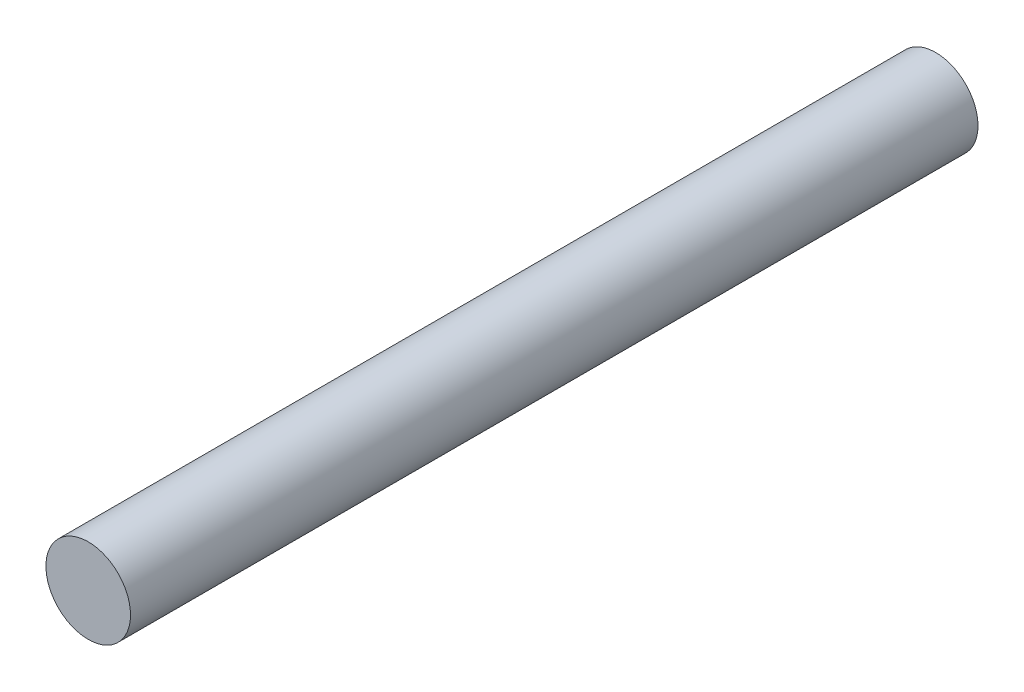
SolidWorks part; units mm, degrees
ref_plane "Front Plane" through (0, 0, 0) normal (0, 0, 1) x (1, 0, 0)
ref_plane "Top Plane" through (0, 0, 0) normal (0, 1, 0) x (1, 0, 0)
ref_plane "Right Plane" through (0, 0, 0) normal (1, 0, 0) x (0, 0, -1)
sketch "Sketch1" plane through (0, 0, 0) normal (0, 0, 1) x (1, 0, 0)
  circle A0 centre (0, 0) radius 1.27
extrude "Extrude1" add sketch "Sketch1" along normal blind 25.4457
sketch "Sketch2" plane through (0, 0, 25.4457) normal (0, 0, 1) x (1, 0, 0)
  line L0 (0, 0) -> (0, 1.27) construction
  circle A0 centre (0, 0) radius 1.27 construction
